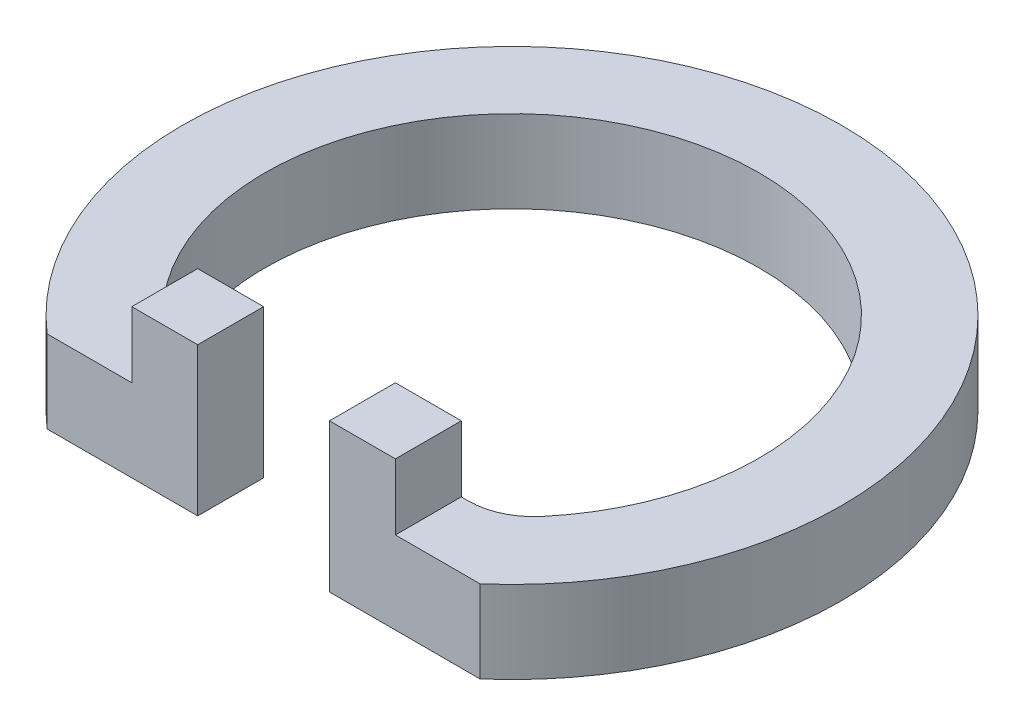
SolidWorks part; units mm, degrees
ref_plane "Front Plane" through (0, 0, 0) normal (0, 0, 1) x (1, 0, 0)
ref_plane "Top Plane" through (0, 0, 0) normal (0, 1, 0) x (1, 0, 0)
ref_plane "Right Plane" through (0, 0, 0) normal (1, 0, 0) x (0, 0, -1)
sketch "Sketch1" plane through (0, 0, 0) normal (0, 1, 0) x (1, 0, 0)
  circle A0 centre (0, 0) radius 50.8
  dimension "D1" = 101.6
extrude "Boss-Extrude1" add sketch "Sketch1" along normal blind 12.7
sketch "Sketch2" plane through (0, 12.7, 0) normal (0, 1, 0) x (1, 0, 0)
  line L0 (-25.6892, -28.1367) -> (-10.16, -28.1367)
  line L1 (-10.16, -28.1367) -> (-10.16, -38.2967)
  line L2 (-10.16, -38.2967) -> (-33.3767, -38.2967)
  line L5 (0, 0) -> (0, -66.5559) construction
  line L6 (10.16, -38.2967) -> (33.3767, -38.2967)
  line L7 (10.16, -28.1367) -> (10.16, -38.2967)
  line L8 (25.6892, -28.1367) -> (10.16, -28.1367)
  circle A1 centre (0, 0) radius 50.8 construction
  arc A2 (-25.6892, -28.1367) -> (25.6892, -28.1367) centre (0, 0) cw
  arc A3 (-33.3767, -38.2967) -> (33.3767, -38.2967) centre (0, 0) ccw
  dimension "D1" = 38.1
  dimension "D2" = 10.16
  dimension "D3" = 10.16
extrude "Cut-Extrude1" cut sketch "Sketch2" against normal blind 12.7
sketch "Sketch3" plane through (-12.7, 12.7, 0) normal (0, -1, 0) x (0, 0, -1)
  line L5 (-28.1367, -12.9892) -> (-28.1367, 2.54) construction
  line L6 (-28.1367, -7.62) -> (-38.2967, -7.62)
  line L7 (-28.1367, -7.62) -> (-28.1367, 2.54)
  line L8 (-28.1367, 2.54) -> (-38.2967, 2.54)
  line L9 (-38.2967, -7.62) -> (-38.2967, 2.54)
  dimension "D1" = 10.16
extrude "Boss-Extrude2" add sketch "Sketch3" against normal blind 10.16
fillet "Fillet1" radius 10.16 1 edges at (-25.6892, 6.35, 28.1367)
mirror "Mirror1" about plane through (0, 0, 0) normal (1, 0, 0) of "Boss-Extrude2"
fillet "Fillet2" radius 10.16 1 edges at (25.6892, 6.35, 28.1367)
